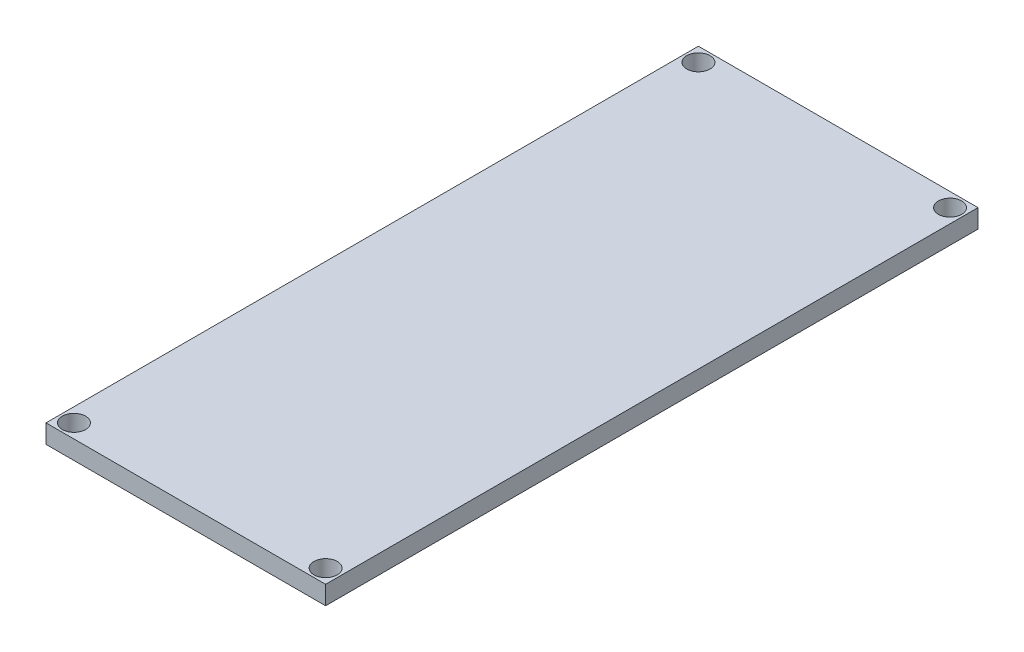
SolidWorks part; units mm, degrees
ref_plane "Front Plane" through (0, 0, 0) normal (0, 0, 1) x (1, 0, 0)
ref_plane "Top Plane" through (0, 0, 0) normal (0, 1, 0) x (1, 0, 0)
ref_plane "Right Plane" through (0, 0, 0) normal (1, 0, 0) x (0, 0, -1)
sketch "Sketch1" plane through (0, 0, 0) normal (0, 1, 0) x (1, 0, 0)
  line L1 (15, -35) -> (-15, -35)
  line L2 (15, -35) -> (15, 35)
  line L3 (15, 35) -> (-15, 35)
  line L4 (-15, -35) -> (-15, 35)
  line L5 (15, -35) -> (-15, 35) construction
  line L6 (15, 35) -> (-15, -35) construction
  point P0 (0, 0)
  dimension "D1" = 30
  dimension "D2" = 70
extrude "Boss-Extrude1" add sketch "Sketch1" along normal blind 2
sketch "Sketch2" plane through (0, 2, 0) normal (0, 1, 0) x (1, 0, 0)
  line L0 (15, 0) -> (-15, 0) construction
  line L1 (-15, 35) -> (-15, -35) construction
  line L2 (0, -35) -> (0, 35) construction
  line L3 (15, 35) -> (-15, 35) construction
  circle A0 centre (-13.5, 33.5) radius 1.25
  circle A1 centre (13.5, 33.5) radius 1.25
  circle A2 centre (13.5, -33.5) radius 1.25
  circle A3 centre (-13.5, -33.5) radius 1.25
  point P6 (0, 0)
  point P12 (0, 0)
  point P14 (0, 0)
  point P16 (-12.3206, 33.0554)
  dimension "D1" = 2.5
  dimension "D2" = 1.5
  dimension "D3" = 1.5
extrude "Cut-Extrude1" cut sketch "Sketch2" against normal up to surface (2 mm away) up to face at (0, 0, 0)
